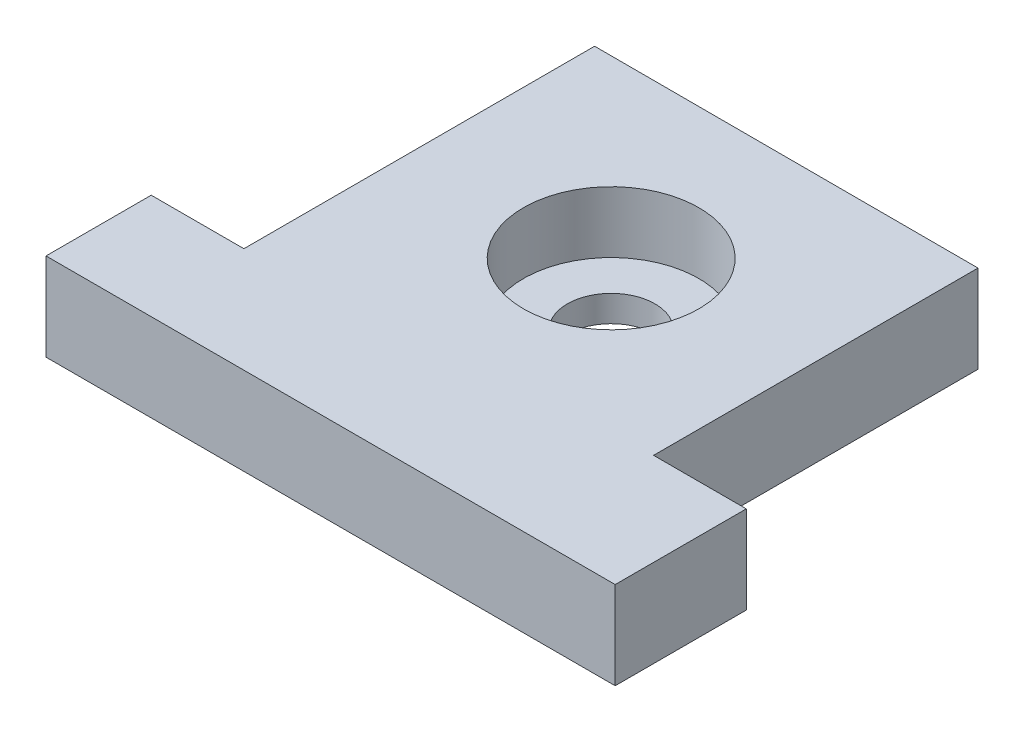
SolidWorks part; units mm, degrees
material "6061 Alloy"
ref_plane "Front Plane" through (0, 0, 0) normal (0, 0, 1) x (1, 0, 0)
ref_plane "Top Plane" through (0, 0, 0) normal (0, 1, 0) x (1, 0, 0)
ref_plane "Right Plane" through (0, 0, 0) normal (1, 0, 0) x (0, 0, -1)
sketch "Sketch1" plane through (0, 0, 0) normal (0, 1, 0) x (1, 0, 0)
  line L0 (-32.4586, 0) -> (32.4586, 0)
  line L1 (-32.4586, 0) -> (-32.4586, 12)
  line L2 (32.4586, 0) -> (32.4586, 14.9524)
  line L3 (-32.4586, 12) -> (-21.8871, 12)
  line L4 (32.4586, 14.9524) -> (21.8871, 14.9524)
  line L5 (-21.8871, 12) -> (-21.8871, 52)
  line L6 (21.8871, 14.9524) -> (21.8871, 51.9524)
  line L7 (-21.8871, 52) -> (21.8871, 51.9524)
  line L8 (21.8871, 51.9524) -> (21.8719, 52.0307)
  point P4 (0, 0)
  dimension "D1" = 40
  dimension "D2" = 12
extrude "Boss-Extrude1" add sketch "Sketch1" along normal blind 10 contours L7 L5 L3 L1 L0 L2 L4 L6
sketch "Sketch2" plane through (0, 10, 0) normal (0, 1, 0) x (1, 0, 0)
  line L0 (-32.4586, 0) -> (32.4586, 0) construction
  circle A0 centre (0, 32) radius 10
  dimension "D1" = 32
extrude "Cut-Extrude2" cut sketch "Sketch2" against normal blind 7
sketch "Sketch5" plane through (0, 3, 0) normal (0, 1, 0) x (1, 0, 0)
  circle A0 centre (0, 32) radius 5
extrude "Cut-Extrude3" cut sketch "Sketch5" against normal through all
